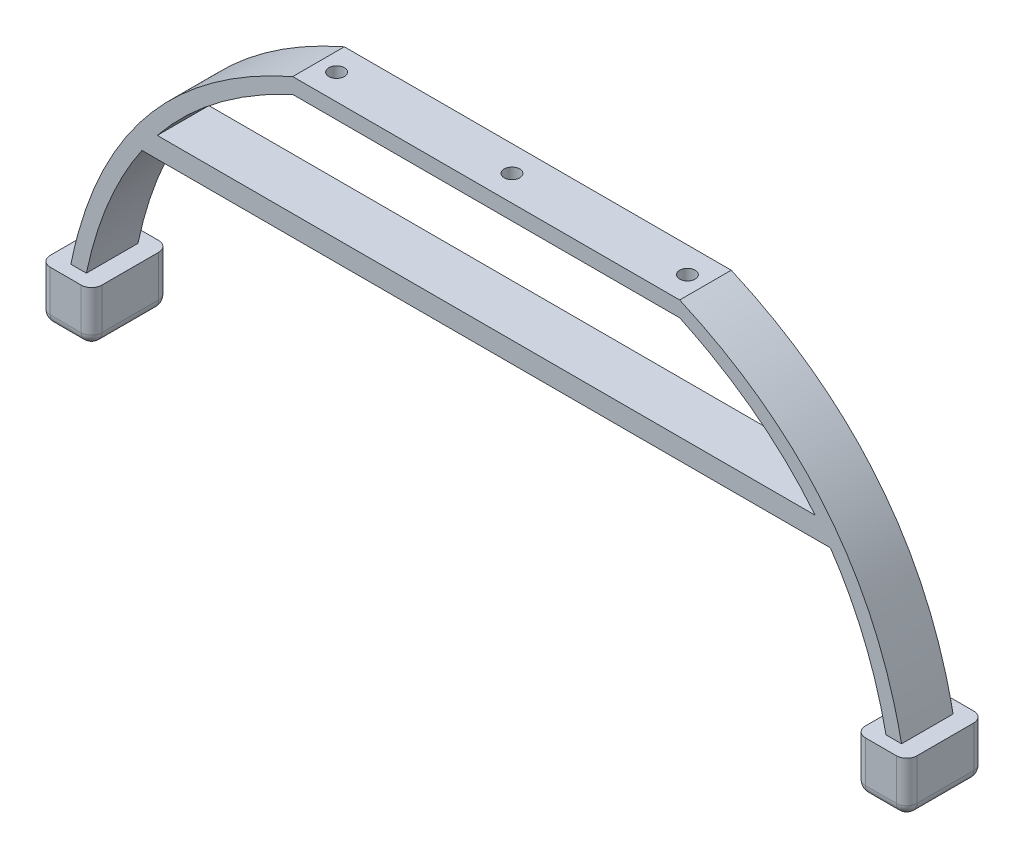
SolidWorks part; units mm, degrees
ref_plane "Front Plane" through (0, 0, 0) normal (0, 0, 1) x (1, 0, 0)
ref_plane "Top Plane" through (0, 0, 0) normal (0, 1, 0) x (1, 0, 0)
ref_plane "Right Plane" through (0, 0, 0) normal (1, 0, 0) x (0, 0, -1)
sketch "Sketch1" plane through (0, 0, 0) normal (0, 0, 1) x (1, 0, 0)
  line L0 (0, 0) -> (75, 0)
  line L1 (0, 0) -> (0, -3)
  line L2 (0, -3) -> (75, -3)
  line L3 (75, -3) -> (75, 0)
  line L4 (0, -53) -> (81.582, -53) construction
  line L5 (102.9064, -25.1487) -> (105, -23)
  line L6 (115, -53) -> (118, -53)
  line L7 (37.5, 0) -> (37.5, -31.7491) construction
  line L8 (-40, -53) -> (-43, -53)
  line L9 (-27.9115, -25.1536) -> (-30, -23)
  line L10 (101.2524, -23) -> (-26.2539, -23)
  line L11 (104.22, -27) -> (-29.2214, -27)
  spline S0 degree 2 poles (-40, -53) (-32.7053, -18.2462) (0, -3) knots 0 0 0 1 1 1
  spline S1 degree 2 poles (75, 0) (110.4585, -15.6037) (118, -53) knots 0 0 0 1 1 1
  spline S2 degree 2 poles (0, 0) (-35.4585, -15.6037) (-43, -53) knots 0 0 0 1 1 1
  spline S3 degree 2 poles (115, -53) (107.7029, -18.2469) (75, -3) knots 0 0 0 1 1 1
  point P13 (37.5, 0)
  dimension "D1" = 75
  dimension "D2" = 3
  dimension "D3" = 50
  dimension "D4" = 30
  dimension "D5" = 20
  dimension "D6" = 40
  dimension "D7" = 4
  dimension "D8" = 127.5064
extrude "Boss-Extrude1" add sketch "Sketch1" along normal blind 10
sketch "Sketch2" plane through (0, 0, 0) normal (0, 1, 0) x (1, 0, 0)
  line L0 (75, -10) -> (75, 0) construction
  line L1 (75, -5) -> (-7.7429, -5) construction
  line L2 (0, -10) -> (0, 0) construction
  circle A0 centre (71.5, -5) radius 1.5
  circle A1 centre (3.5, -5) radius 1.5
  circle A2 centre (37.5, -5) radius 1.5
  point P0 (75, -5)
  dimension "D3" = 3
  dimension "D4" = 3
  dimension "D1" = 68
  dimension "D2" = 3.5
  dimension "D5" = 37.5
extrude "Cut-Extrude1" cut sketch "Sketch2" against normal blind 10
sketch "Sketch3" plane through (0, -53, 0) normal (0, -1, 0) x (1, 0, 0)
  line L1 (115, 0) -> (118, 0) construction
  line L2 (37.5, 5) -> (37.5, -34.9433) construction
  line L3 (121.5, 12.5) -> (111.5, 12.5)
  line L4 (121.5, 12.5) -> (121.5, -2.5)
  line L5 (121.5, -2.5) -> (111.5, -2.5)
  line L6 (111.5, 12.5) -> (111.5, -2.5)
  line L7 (121.5, 12.5) -> (111.5, -2.5) construction
  line L8 (121.5, -2.5) -> (111.5, 12.5) construction
  line L9 (-36.5, 12.5) -> (-36.5, -2.5)
  line L10 (-46.5, -2.5) -> (-36.5, -2.5)
  line L11 (-46.5, 12.5) -> (-36.5, 12.5)
  line L12 (-46.5, 12.5) -> (-46.5, -2.5)
  line L13 (115, 10) -> (115, 0) construction
  point P0 (76.3519, 5)
  point P1 (116.5, 0)
  point P4 (116.5, 5)
  point P7 (116.5, 5)
  point P12 (37.5, 5)
  point P20 (115, 5)
  dimension "D1" = 10
  dimension "D2" = 15
extrude "Boss-Extrude2" add sketch "Sketch3" along normal blind 10
fillet "Fillet1" radius 2 8 edges at (111.5, -58, 12.5) (116.5, -63, 12.5) (121.5, -63, 5) (121.5, -58, 12.5) (121.5, -58, -2.5) (111.5, -63, 5) (116.5, -63, -2.5) (111.5, -58, -2.5)
fillet "Fillet2" radius 2 8 edges at (-36.5, -58, 12.5) (-46.5, -58, 12.5) (-41.5, -63, 12.5) (-46.5, -63, 5) (-46.5, -58, -2.5) (-41.5, -63, -2.5) (-36.5, -58, -2.5) (-36.5, -63, 5)
